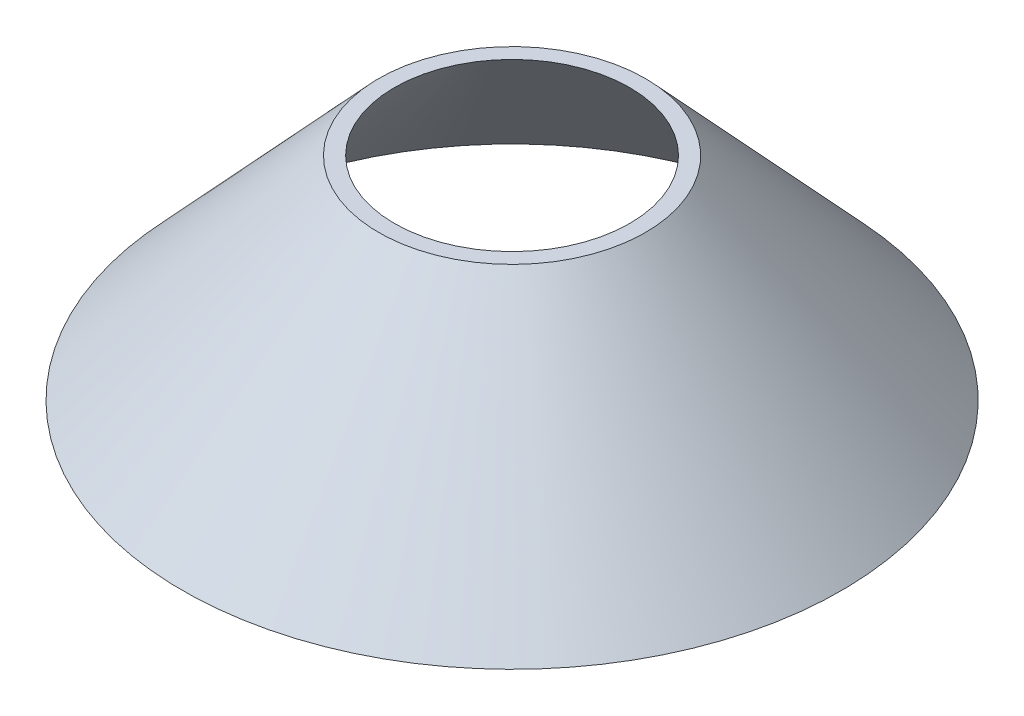
SolidWorks part; units mm, degrees
ref_plane "Front Plane" through (0, 0, 0) normal (0, 0, 1) x (1, 0, 0)
ref_plane "Top Plane" through (0, 0, 0) normal (0, 1, 0) x (1, 0, 0)
ref_plane "Right Plane" through (0, 0, 0) normal (1, 0, 0) x (0, 0, -1)
sketch "Sketch1" plane through (0, 0, 0) normal (0, 0, 1) x (1, 0, 0)
  line L0 (0, 0) -> (0, 150.6605) construction
  line L1 (53.34, 0) -> (50.8, 0)
  line L2 (0, 30.1879) -> (25.4, 30.1879) construction
  line L3 (0, 0) -> (53.34, 0) construction
  line L4 (53.34, 0) -> (25.4, 30.1879)
  line L5 (25.4, 30.1879) -> (21.59, 34.3044)
  line L9 (50.8, 0) -> (19.05, 34.3044)
  line L10 (19.05, 34.3044) -> (21.59, 34.3044)
  line L11 (19.05, 34.3044) -> (0, 34.3044) construction
  dimension "D1" = 53.34
  dimension "D2" = 25.4
  dimension "D3" = 2.54
  dimension "D4" = 30.1879
revolve "Revolve1" add sketch "Sketch1" angle 360 about L0
